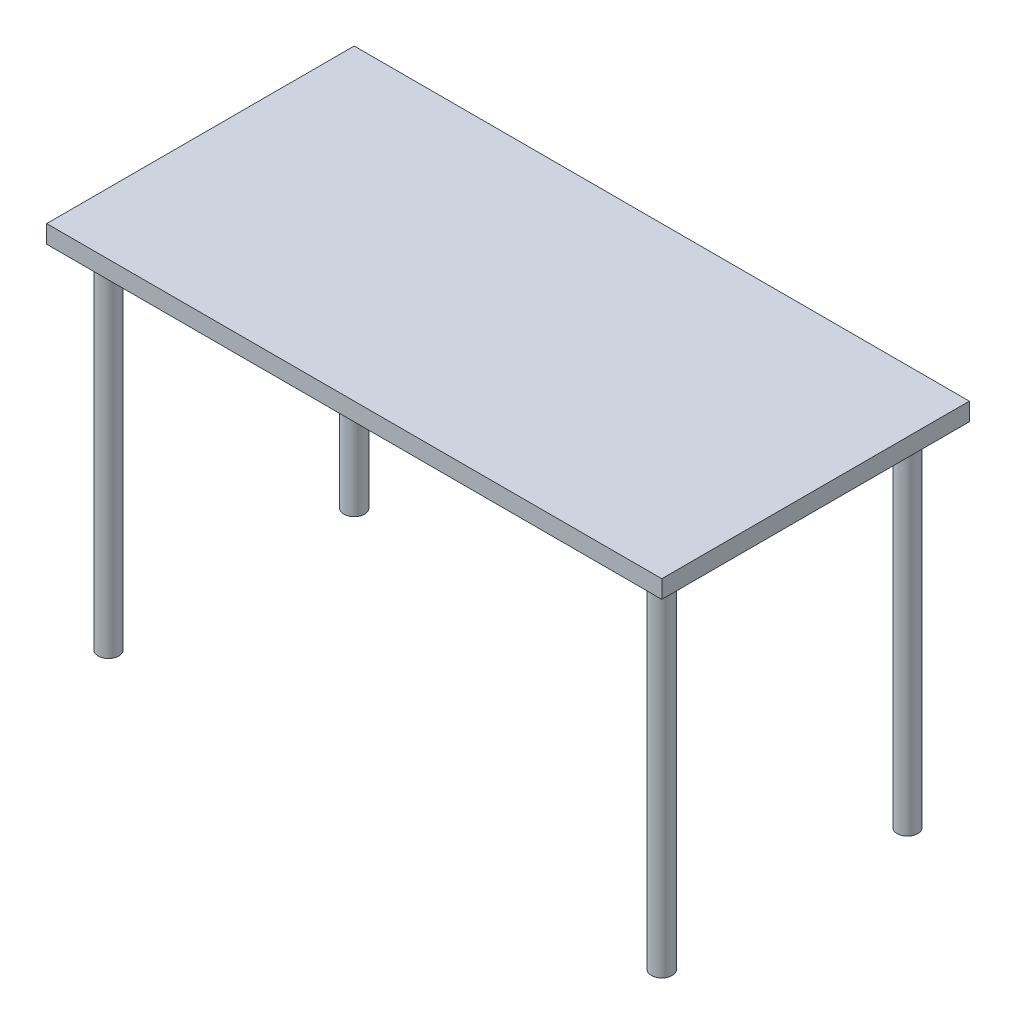
SolidWorks part; units mm, degrees
ref_plane "Front Plane" through (0, 0, 0) normal (0, 0, 1) x (1, 0, 0)
ref_plane "Top Plane" through (0, 0, 0) normal (0, 1, 0) x (1, 0, 0)
ref_plane "Right Plane" through (0, 0, 0) normal (1, 0, 0) x (0, 0, -1)
sketch "Sketch1" plane through (0, 0, 0) normal (0, 1, 0) x (1, 0, 0)
  line L1 (600.075, -300.0375) -> (-600.075, -300.0375)
  line L2 (600.075, -300.0375) -> (600.075, 300.0375)
  line L3 (600.075, 300.0375) -> (-600.075, 300.0375)
  line L4 (-600.075, -300.0375) -> (-600.075, 300.0375)
  line L5 (600.075, -300.0375) -> (-600.075, 300.0375) construction
  line L6 (600.075, 300.0375) -> (-600.075, -300.0375) construction
  point P0 (0, 0)
  dimension "D1" = 600.075
  dimension "D2" = 1200.15
extrude "Boss-Extrude1" add sketch "Sketch1" along normal blind 34.925
sketch "Sketch2" plane through (0, 0, 0) normal (0, -1, 0) x (1, 0, 0)
  line L0 (-600.075, -300.0375) -> (-600.075, 300.0375) construction
  line L1 (-600.075, 300.0375) -> (600.075, 300.0375) construction
  line L2 (600.075, 300.0375) -> (600.075, -300.0375) construction
  line L3 (600.075, -300.0375) -> (-600.075, -300.0375) construction
  circle A0 centre (-539.75, 239.7125) radius 20.213
  circle A2 centre (539.75, 239.7125) radius 20.213
  circle A3 centre (-539.75, -239.7125) radius 20.213
  circle A4 centre (539.75, -239.7125) radius 20.213
  dimension "D1" = 40.426
  dimension "D4" = 40.426
  dimension "D8" = 40.426
  dimension "D10" = 40.426
  dimension "D2" = 60.325
  dimension "D3" = 60.325
  dimension "D5" = 60.325
  dimension "D6" = 60.325
  dimension "D7" = 60.325
  dimension "D9" = 60.325
extrude "Boss-Extrude2" add sketch "Sketch2" along normal blind 685.8
sketch "Sketch3" plane through (0, 0, 0) normal (0, -1, 0) x (1, 0, 0)
  circle A0 centre (-539.75, 239.7125) radius 51.963
  circle A2 centre (-539.75, 239.7125) radius 20.213 construction
  circle A4 centre (539.75, 239.7125) radius 51.963
  circle A5 centre (539.75, 239.7125) radius 20.213 construction
  circle A6 centre (539.75, -239.7125) radius 51.963
  circle A7 centre (539.75, -239.7125) radius 20.213 construction
  circle A8 centre (-539.75, -239.7125) radius 51.963
  circle A9 centre (-539.75, -239.7125) radius 20.213 construction
  dimension "D1" = 31.75
  dimension "D2" = 31.75
  dimension "D3" = 31.75
  dimension "D4" = 31.75
extrude "Boss-Extrude3" add sketch "Sketch3" along normal blind 1.5875
